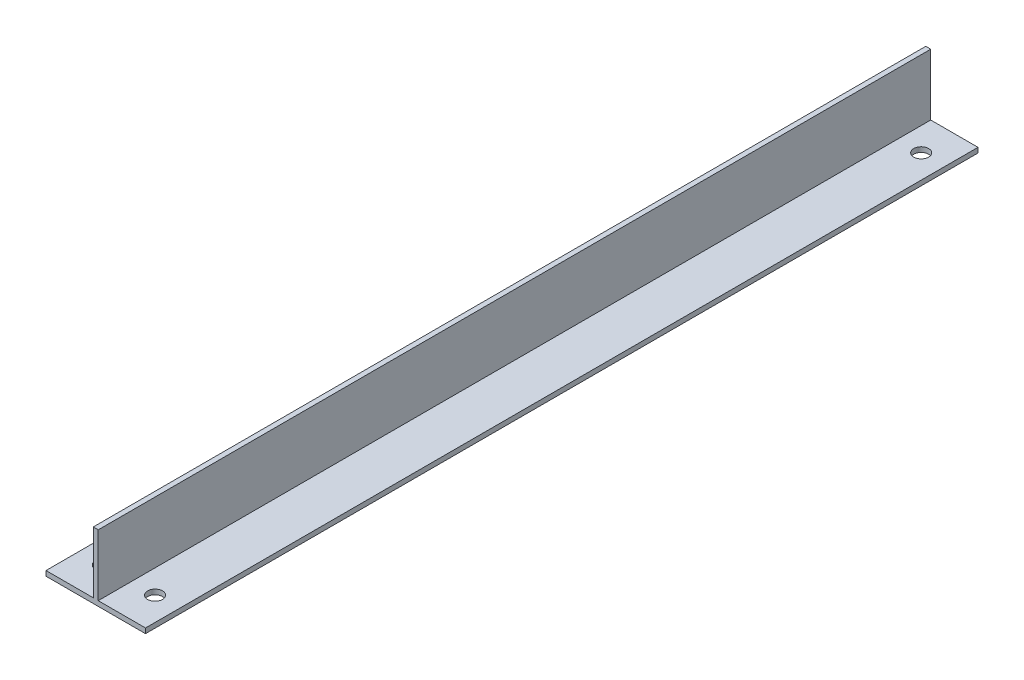
SolidWorks part; units mm, degrees
material "1060 Сплав"
ref_plane "Спереди" through (0, 0, 0) normal (0, 0, 1) x (1, 0, 0)
ref_plane "Сверху" through (0, 0, 0) normal (0, 1, 0) x (1, 0, 0)
ref_plane "Справа" through (0, 0, 0) normal (1, 0, 0) x (0, 0, -1)
sketch "Эскиз1" plane through (0, 0, 0) normal (0, 0, 1) x (1, 0, 0)
  line L0 (0, 0) -> (0, 18.5)
  line L1 (0, 18.5) -> (1.5, 18.5)
  line L2 (1.5, 18.5) -> (1.5, 0)
  line L3 (1.5, 0) -> (15.75, 0)
  line L4 (15.75, 0) -> (15.75, -1.5)
  line L5 (15.75, -1.5) -> (-14.25, -1.5)
  line L6 (-14.25, -1.5) -> (-14.25, 0)
  line L7 (-14.25, 0) -> (0, 0)
  dimension "D1" = 30
  dimension "D2" = 20
  dimension "D3" = 1.5
extrude "Бобышка-Вытянуть1" add sketch "Эскиз1" along normal blind 251
sketch "Эскиз2" plane through (0, 0, 0) normal (0, 1, 0) x (1, 0, 0)
  line L0 (8.625, 0) -> (8.625, -251) construction
  line L1 (15.75, 0) -> (1.5, 0) construction
  line L2 (15.75, -251) -> (1.5, -251) construction
  line L3 (-7.125, -251) -> (-7.125, 0) construction
  line L4 (0, -251) -> (-14.25, -251) construction
  line L5 (0, 0) -> (-14.25, 0) construction
  line L6 (-7.125, -10) -> (8.625, -10) construction
  line L7 (-7.125, -241) -> (8.625, -241) construction
  circle A0 centre (-7.125, -10) radius 2.25
  circle A1 centre (8.625, -10) radius 2.25
  circle A2 centre (-7.125, -241) radius 2.25
  circle A3 centre (8.625, -241) radius 2.25
  dimension "D1" = 10
  dimension "D2" = 4.5
  dimension "D3" = 10
extrude "Вырез-Вытянуть1" cut sketch "Эскиз2" against normal through all
